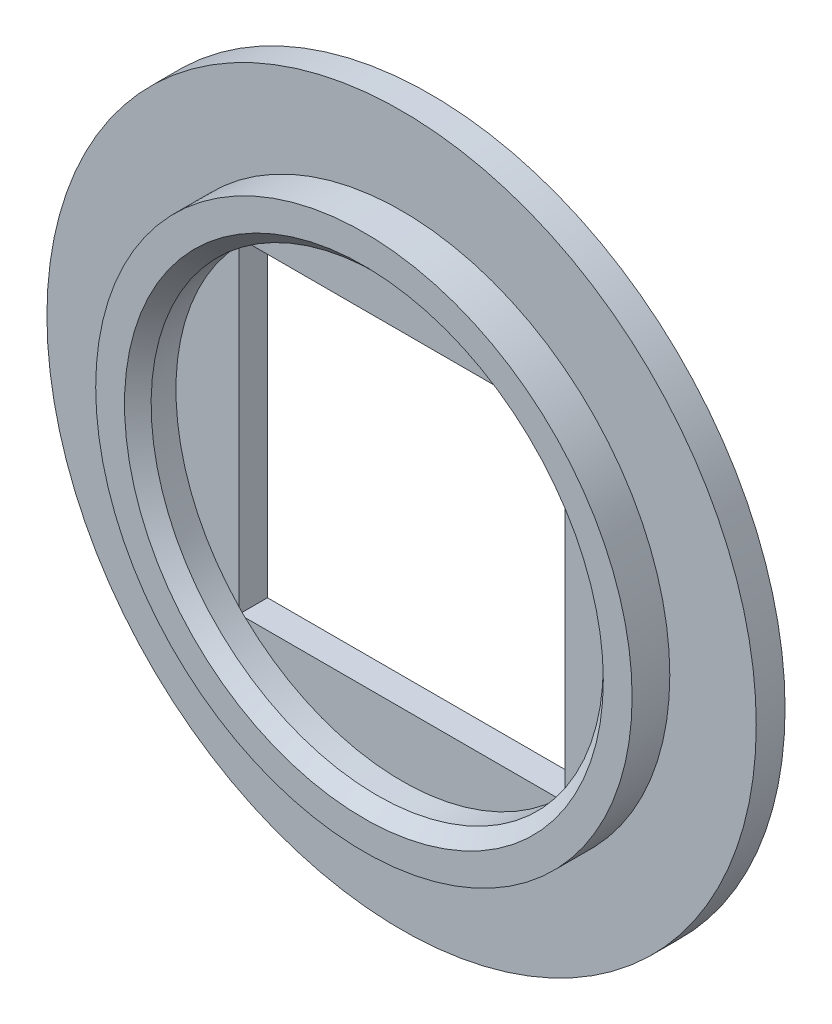
SolidWorks part; units mm, degrees
ref_plane "前视基准面" through (0, 0, 0) normal (0, 0, 1) x (1, 0, 0)
ref_plane "上视基准面" through (0, 0, 0) normal (0, 1, 0) x (1, 0, 0)
ref_plane "右视基准面" through (0, 0, 0) normal (1, 0, 0) x (0, 0, -1)
sketch "草图1" plane through (0, 0, 0) normal (0, 0, 1) x (1, 0, 0)
  circle A0 centre (0, 0) radius 8
extrude "凸台-拉伸1" add sketch "草图1" along normal blind 0.65
sketch "草图2" plane through (0, 0, 0) normal (0, 0, 1) x (1, 0, 0)
  circle A0 centre (0, 0) radius 6.05
  circle A1 centre (0, 0) radius 5.1
extrude "凸台-拉伸2" add sketch "草图2" along normal blind 0.85 from surface at 0.65 starting at face at (8, 0, 0.65)
sketch "草图3" plane through (0, 0, 0) normal (0, 0, 1) x (1, 0, 0)
  circle A0 centre (0, 0) radius 5.1
extrude "切除-拉伸1" cut sketch "草图3" against normal blind 0.01 from surface at 0.65 starting at face at (6.05, 0, 0.65)
sketch "草图4" plane through (0, 0, 0) normal (0, 0, 1) x (1, 0, 0)
  line L1 (3.675, 3.675) -> (3.675, -3.675)
  line L3 (-3.675, 3.675) -> (3.675, 3.675)
  line L13 (3.675, -3.675) -> (-3.675, -3.675)
  line L14 (-3.675, 0) -> (-3.675, -3.675)
  line L15 (-3.675, 0) -> (-3.675, 3.675)
extrude "切除-拉伸2" cut sketch "草图4" along normal up to surface (0.64 mm away) up to face at (5.1, 0, 0.64)
chamfer "倒角1" distance 0.3 angle 45 1 edges at (5.1, 0, 1.5)
